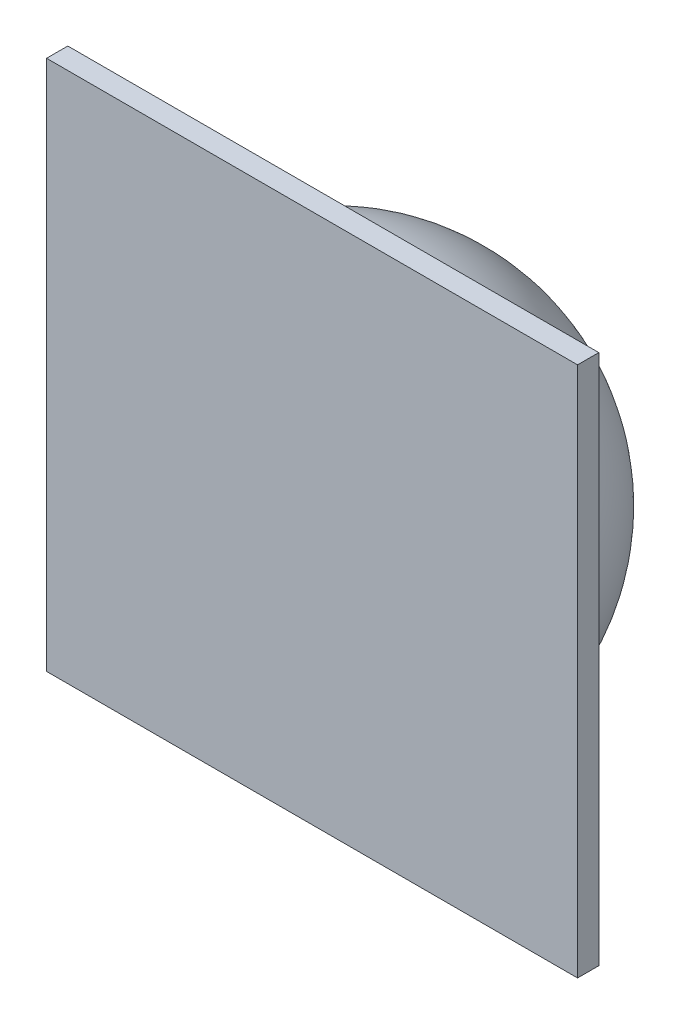
SolidWorks part; units mm, degrees
ref_plane "Front Plane" through (0, 0, 0) normal (0, 0, 1) x (1, 0, 0)
ref_plane "Top Plane" through (0, 0, 0) normal (0, 1, 0) x (1, 0, 0)
ref_plane "Right Plane" through (0, 0, 0) normal (1, 0, 0) x (0, 0, -1)
sketch "Sketch1" plane through (0, 0, 0) normal (0, 0, 1) x (1, 0, 0)
  line L1 (-25, -25) -> (25, -25)
  line L2 (-25, -25) -> (-25, 25)
  line L3 (-25, 25) -> (25, 25)
  line L4 (25, -25) -> (25, 25)
  line L5 (-25, -25) -> (25, 25) construction
  line L6 (-25, 25) -> (25, -25) construction
  point P0 (0, 0)
  dimension "D1" = 50
  dimension "D2" = 50
extrude "Boss-Extrude1" add sketch "Sketch1" along normal blind 2
sketch "Sketch2" plane through (0, 0, 0) normal (1, 0, 0) x (0, 0, -1)
  line L0 (18, 0) -> (20, 0) construction
  line L1 (0, -25) -> (0, 25) construction
  line L2 (0, -20) -> (0, -18)
  line L3 (18, 0) -> (20, 0)
  arc A0 (0, -20) -> (20, 0) centre (0, 0) ccw
  arc A1 (0, -18) -> (18, 0) centre (0, 0) ccw
  dimension "D2" = 36
  dimension "D1" = 20
revolve "Revolve2" add sketch "Sketch2" angle 360 about L0
scale "Scale1" scale about centroid uniform scaling yes scale factor 0.5
scale "Scale2" scale about centroid uniform scaling yes scale factor 0.6
sketch "Sketch3" plane through (0, 0, -2.8039) normal (0, 0, -1) x (-1, 0, 0)
  line L1 (-1, -1) -> (1, -1)
  line L2 (-1, -1) -> (-1, 1)
  line L3 (-1, 1) -> (1, 1)
  line L4 (1, -1) -> (1, 1)
  line L5 (-1, -1) -> (1, 1) construction
  line L6 (-1, 1) -> (1, -1) construction
  point P0 (0, 0)
  dimension "D1" = 2
  dimension "D2" = 2
extrude "Boss-Extrude2" add sketch "Sketch3" along normal blind 2
